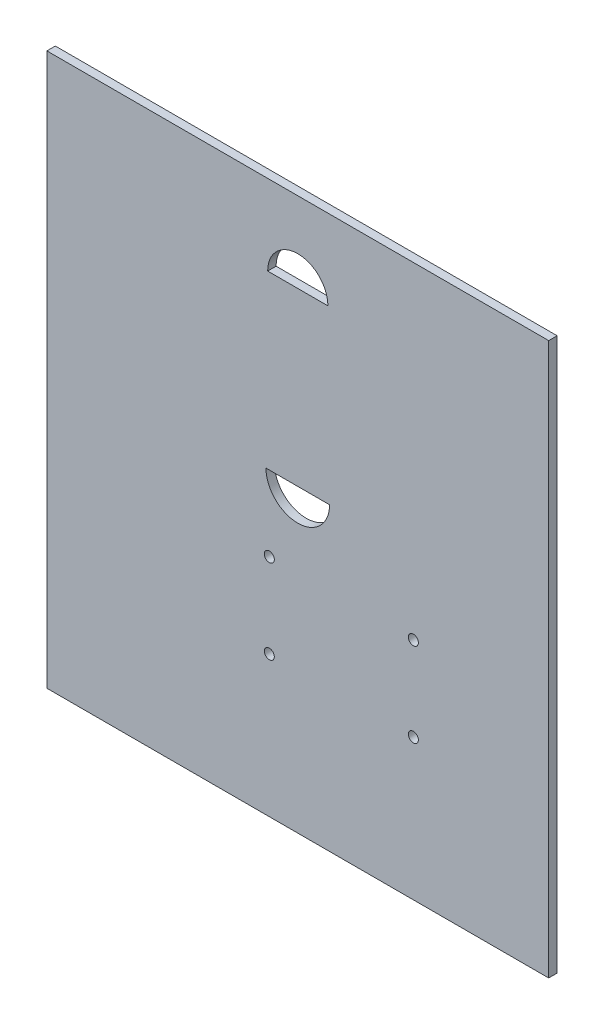
SolidWorks part; units mm, degrees
ref_plane "Plan de face" through (0, 0, 0) normal (0, 0, 1) x (1, 0, 0)
ref_plane "Plan de dessus" through (0, 0, 0) normal (0, 1, 0) x (1, 0, 0)
ref_plane "Plan de droite" through (0, 0, 0) normal (1, 0, 0) x (0, 0, -1)
sketch "Sketch1" plane through (0, 0, 0) normal (0, 0, 1) x (1, 0, 0)
  line L1 (-220.2282, 110.1141) -> (29.7718, 110.1141)
  line L2 (-220.2282, 110.1141) -> (-220.2282, -164.8859)
  line L3 (-220.2282, -164.8859) -> (29.7718, -164.8859)
  line L4 (29.7718, 110.1141) -> (29.7718, -164.8859)
  dimension "D1" = 275
  dimension "D2" = 250
extrude "Boss-Extrude1" add sketch "Sketch1" along normal blind 4.2
sketch "Esquisse1" plane through (0, 0, 4.2) normal (0, 0, 1) x (1, 0, 0)
  line L0 (-220.2282, 110.1141) -> (-220.2282, -164.8859) construction
  line L1 (-110.2282, 70.1141) -> (-80.2282, 70.1141)
  line L2 (29.7718, 110.1141) -> (-220.2282, 110.1141) construction
  line L5 (-111.0739, -15.3059) -> (-79.3825, -15.3059)
  arc A1 (-110.2282, 70.1141) -> (-80.2282, 70.1141) centre (-95.2282, 70.1141) cw
  arc A3 (-111.0739, -15.3059) -> (-79.3825, -15.3059) centre (-95.2282, -15.3059) ccw
  circle A4 centre (-37.6557, -94.6492) radius 2.5
  circle A5 centre (-37.6557, -52.7392) radius 2.5
  circle A6 centre (-109.4107, -94.6492) radius 2.5
  circle A7 centre (-109.4107, -52.7392) radius 2.5
  dimension "D2" = 15
  dimension "D4" = 85.42
  dimension "D1" = 125
  dimension "D3" = 40
  dimension "D5" = 0
  dimension "D6" = 41.91
  dimension "D7" = 71.755
  dimension "D8" = 41.91
  dimension "D9" = 71.755
  dimension "D10" = 83.0977
  dimension "D11" = 83.0977
extrude "Enlèv. mat.-Extru.1" cut sketch "Esquisse1" against normal through all
